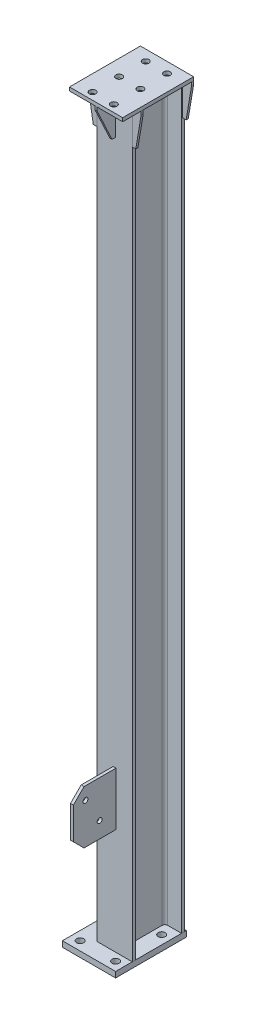
SolidWorks part; units mm, degrees
material "普通碳钢"
ref_plane "前视基准面" through (0, 0, 0) normal (0, 0, 1) x (1, 0, 0)
ref_plane "上视基准面" through (0, 0, 0) normal (0, 1, 0) x (1, 0, 0)
ref_plane "右视基准面" through (0, 0, 0) normal (1, 0, 0) x (0, 0, -1)
sketch "草图1" plane through (0, 0, 0) normal (1, 0, 0) x (0, 0, -1)
  line L0 (-4877.1272, -1126.8159) -> (-4877.1272, -3226.8159)
  dimension "D1" = 2100
other "H型钢 HM150×100(1)"
ref_plane "基准面4" through (-50, -1126.8159, 4951.1272) normal (0, -1, 0) x (1, 0, 0)
sketch "草图11" plane through (-50, -1126.8159, 4951.1272) normal (0, -1, 0) x (1, 0, 0)
  line L0 (-50, -74) -> (50, -74)
  line L1 (50, -74) -> (50, -65)
  line L2 (50, -65) -> (11, -65)
  line L3 (3, -57) -> (3, 57)
  line L4 (11, 65) -> (50, 65)
  line L5 (50, 65) -> (50, 74)
  line L6 (50, 74) -> (-50, 74)
  line L7 (0, 74) -> (0, -74) construction
  line L11 (0, 60) -> (0, 74) construction
  line L14 (-50, -74) -> (-50, -65)
  line L15 (-50, -65) -> (-11, -65)
  line L16 (-3, -57) -> (-3, 57)
  line L17 (-11, 65) -> (-50, 65)
  line L18 (-50, 65) -> (-50, 74)
  arc A2 (11, -65) -> (3, -57) centre (11, -57) cw
  arc A3 (3, 57) -> (11, 65) centre (11, 57) cw
  arc A5 (-11, -65) -> (-3, -57) centre (-11, -57) ccw
  arc A6 (-3, 57) -> (-11, 65) centre (-11, 57) ccw
  point P2 (0, 0)
  point P38 (0, 0)
  point P39 (50, 74)
  point P40 (50, -74)
  point P41 (-50, -74)
  dimension "D8" = 8
  dimension "D1" = 6
  dimension "D2" = 9
  dimension "D3" = 148
  dimension "D4" = 100
  dimension "D9" = 0
sketch "草图12" plane through (0, -3226.8159, 0) normal (0, -1, 0) x (1, 0, 0)
  line L0 (0, 5016.1272) -> (0, 5025.1272) construction
  line L1 (0, 5072.1272) -> (-150, 5072.1272)
  line L2 (0, 5072.1272) -> (0, 4872.1272)
  line L3 (0, 4872.1272) -> (-150, 4872.1272)
  line L4 (-150, 5072.1272) -> (-150, 4872.1272)
  line L5 (-100, 4877.1272) -> (0, 4877.1272) construction
  dimension "D1" = 5
  dimension "D2" = 200
  dimension "D3" = 150
extrude "凸台-拉伸1" add sketch "草图12" along normal blind 16 separate body contours L1 L4 L3 L2
sketch "草图13" plane through (-100, 0, 0) normal (-1, 0, 0) x (0, 0, 1)
  line L0 (5025.1272, -3226.8159) -> (5025.1272, -1126.8159) construction
  line L1 (4877.1272, -1126.8159) -> (5025.1272, -1126.8159)
  line L2 (4877.1272, -1126.8159) -> (4877.1272, -1136.8159)
  line L3 (4877.1272, -1136.8159) -> (5025.1272, -1136.8159)
  line L4 (5025.1272, -1126.8159) -> (5025.1272, -1136.8159)
  dimension "D1" = 10
extrude "切除-拉伸1" cut sketch "草图13" against normal up to vertex (100 mm away) up to point (0, -1126.8159, 4877.1272)
sketch "草图14" plane through (0, -1136.8159, 0) normal (0, 1, 0) x (1, 0, 0)
  line L0 (-100, -4877.1272) -> (-100, -4886.1272) construction
  line L1 (25, -5077.1272) -> (-125, -5077.1272)
  line L2 (25, -5077.1272) -> (25, -4877.1272)
  line L3 (25, -4877.1272) -> (-125, -4877.1272)
  line L4 (-125, -5077.1272) -> (-125, -4877.1272)
  line L5 (0, -4877.1272) -> (-100, -4877.1272) construction
  dimension "D1" = 150
  dimension "D2" = 200
  dimension "D3" = 25
extrude "凸台-拉伸2" add sketch "草图14" along normal blind 10 separate body
sketch "草图16" plane through (0, -1126.8159, 0) normal (0, 1, 0) x (1, 0, 0)
  line L0 (-50, -4877.1272) -> (-50, -5077.1272) construction
  line L1 (25, -4877.1272) -> (-125, -4877.1272) construction
  line L2 (-125, -5077.1272) -> (25, -5077.1272) construction
  line L3 (25, -4907.1272) -> (-125, -4907.1272) construction
  line L4 (25, -5077.1272) -> (25, -4877.1272) construction
  line L5 (-125, -4877.1272) -> (-125, -5077.1272) construction
  line L6 (25, -4982.1272) -> (-125, -4982.1272) construction
  line L7 (25, -5057.1272) -> (4128.0739, -5057.1272) construction
  line L8 (-20, -4877.1272) -> (-20, -5078.3146) construction
  line L9 (-80, -4877.1272) -> (-80, -5078.3146) construction
  circle A0 centre (-20, -4907.1272) radius 9
  circle A1 centre (-20, -4982.1272) radius 9
  circle A2 centre (-20, -5057.1272) radius 9
  circle A3 centre (-80, -4907.1272) radius 9
  circle A4 centre (-80, -4982.1272) radius 9
  circle A5 centre (-80, -5057.1272) radius 9
  dimension "D6" = 18
  dimension "D1" = 30
  dimension "D2" = 30
  dimension "D3" = 30
  dimension "D4" = 75
  dimension "D5" = 75
extrude "切除-拉伸2" cut sketch "草图16" against normal up to next (10 mm away)
sketch "草图17" plane through (0, 0, 4877.1272) normal (0, 0, -1) x (-1, 0, 0)
  line L0 (0, -1136.8159) -> (-25, -1136.8159)
  line L1 (-25, -1136.8159) -> (125, -1136.8159) construction
  line L2 (-25, -1136.8159) -> (-25, -1146.8159)
  line L3 (-25, -1146.8159) -> (-10, -1236.8159)
  line L4 (-10, -1236.8159) -> (0, -1236.8159)
  line L7 (0, -1136.8159) -> (0, -1236.8159)
  line L8 (0, -3226.8159) -> (0, -1136.8159) construction
  line L9 (100, -1136.8159) -> (125, -1136.8159)
  line L10 (125, -1136.8159) -> (125, -1146.8159)
  line L11 (125, -1146.8159) -> (110, -1236.8159)
  line L12 (110, -1236.8159) -> (100, -1236.8159)
  line L13 (100, -3226.8159) -> (100, -1136.8159) construction
  line L14 (100, -1236.8159) -> (100, -1136.8159)
  dimension "D1" = 100
  dimension "D2" = 10
  dimension "D3" = 10
  dimension "D4" = 100
  dimension "D5" = 10
  dimension "D6" = 10
extrude "凸台-拉伸3" add sketch "草图17" against normal blind 6 separate body
sketch "草图18" plane through (0, 0, 5025.1272) normal (0, 0, 1) x (1, 0, 0)
  line L5 (-100, -1236.8159) -> (-100, -1136.8159)
  line L6 (-100, -1136.8159) -> (-125, -1136.8159)
  line L7 (-125, -1136.8159) -> (-125, -1146.8159)
  line L8 (-125, -1146.8159) -> (-110, -1236.8159)
  line L9 (-110, -1236.8159) -> (-100, -1236.8159)
  line L10 (-100, -1236.8159) -> (-100, -1136.8159)
  line L11 (-100, -1136.8159) -> (-125, -1136.8159)
  line L12 (-125, -1136.8159) -> (-125, -1146.8159)
  line L13 (-125, -1146.8159) -> (-110, -1236.8159)
  line L14 (-110, -1236.8159) -> (-100, -1236.8159)
  line L15 (0, -1136.8159) -> (0, -1236.8159)
  line L16 (0, -1236.8159) -> (10, -1236.8159)
  line L17 (10, -1236.8159) -> (25, -1146.8159)
  line L18 (25, -1146.8159) -> (25, -1136.8159)
  line L19 (25, -1136.8159) -> (0, -1136.8159)
  line L20 (0, -1136.8159) -> (0, -1236.8159)
  line L21 (0, -1236.8159) -> (10, -1236.8159)
  line L22 (10, -1236.8159) -> (25, -1146.8159)
  line L23 (25, -1146.8159) -> (25, -1136.8159)
  line L24 (25, -1136.8159) -> (0, -1136.8159)
  dimension "D1" = 0
  dimension "D2" = 0
extrude "凸台-拉伸4" add sketch "草图18" against normal blind 6 separate body
sketch "草图19" plane through (-47, 0, 0) normal (1, 0, 0) x (0, 0, -1)
  line L0 (-5025.1272, -1136.8159) -> (-5077.1272, -1136.8159)
  line L1 (-5077.1272, -1136.8159) -> (-5077.1272, -1146.8159)
  line L2 (-5077.1272, -1146.8159) -> (-5035.1272, -1236.8159)
  line L3 (-5035.1272, -1236.8159) -> (-5025.1272, -1236.8159)
  line L4 (-5025.1272, -1236.8159) -> (-5025.1272, -1146.8159) construction
  line L5 (-5025.1272, -1236.8159) -> (-5025.1272, -1136.8159)
  dimension "D1" = 10
  dimension "D2" = 10
  dimension "D3" = 100
extrude "凸台-拉伸5" add sketch "草图19" against normal up to surface (6 mm away) separate body contours L2 L3 L5 L0 L1 up to face at (-53, -2181.8159, 4951.1272)
sketch "草图20" plane through (0, 0, 5025.1272) normal (0, 0, 1) x (1, 0, 0)
  line L0 (-100, -3226.8159) -> (-100, -1136.8159) construction
  line L1 (-54, -2776.8159) -> (-46, -2776.8159)
  line L2 (-54, -2776.8159) -> (-54, -2926.8159)
  line L3 (-54, -2926.8159) -> (-46, -2926.8159)
  line L4 (-46, -2776.8159) -> (-46, -2926.8159)
  line L5 (0, -3226.8159) -> (-100, -3226.8159) construction
  dimension "D1" = 150
  dimension "D2" = 8
  dimension "D3" = 46
  dimension "D4" = 300
extrude "凸台-拉伸6" add sketch "草图20" along normal blind 120 separate body
chamfer "倒角1" distance 30 angle 45 2 edges at (-50, -2926.8159, 5145.1272) (-50, -2776.8159, 5145.1272)
sketch "草图21" plane through (-46, 0, 0) normal (1, 0, 0) x (0, 0, -1)
  line L0 (-5045.1272, -2926.8159) -> (-5136.3213, -2768.8631) construction
  line L1 (-5115.1272, -2926.8159) -> (-5025.1272, -2926.8159) construction
  line L2 (-5025.1272, -2926.8159) -> (-5025.1272, -2776.8159) construction
  line L5 (-5115.1272, -2881.8159) -> (-5025.1272, -2881.8159)
  line L6 (-5115.1272, -2881.8159) -> (-5025.1272, -2881.8159) construction
  circle A0 centre (-5071.1079, -2881.8159) radius 7
  circle A1 centre (-5111.1079, -2812.5339) radius 7
  dimension "D4" = 14
  dimension "D5" = 14
  dimension "D1" = 60
  dimension "D2" = 20
  dimension "D6" = 80
  dimension "D3" = 45
extrude "切除-拉伸3" cut sketch "草图21" against normal up to next (8 mm away)
sketch "草图22" plane through (0, 0, 4886.1272) normal (0, 0, 1) x (1, 0, 0)
  line L0 (-61, -3226.8159) -> (-61, -1136.8159) construction
  line L1 (-61, -2826.8159) -> (-220, -2826.8159)
  line L2 (-61, -2826.8159) -> (-61, -2976.8159)
  line L3 (-61, -2976.8159) -> (-220, -2976.8159)
  line L4 (-220, -2826.8159) -> (-220, -2976.8159)
  line L5 (-100, -3226.8159) -> (-100, -1136.8159) construction
  line L6 (-61, -3226.8159) -> (-100, -3226.8159) construction
  dimension "D1" = 120
  dimension "D2" = 150
  dimension "D3" = 250
extrude "凸台-拉伸7" add sketch "草图22" along normal blind 8 separate body
chamfer "倒角2" distance 30 angle 45 2 edges at (-220, -2976.8159, 4890.1272) (-220, -2826.8159, 4890.1272)
sketch "草图23" plane through (0, 0, 4894.1272) normal (0, 0, 1) x (1, 0, 0)
  line L0 (-100, -2976.8159) -> (-1212.1791, -1388.4595) construction
  line L1 (-190, -2976.8159) -> (-61, -2976.8159) construction
  line L4 (-100, -3226.8159) -> (-100, -1136.8159) construction
  line L5 (-190, -2936.8159) -> (-61, -2936.8159)
  line L6 (-190, -2936.8159) -> (-61, -2936.8159) construction
  circle A0 centre (-128.0083, -2936.8159) radius 7
  circle A1 centre (-173.8944, -2871.2837) radius 7
  dimension "D3" = 14
  dimension "D4" = 14
  dimension "D5" = 80
  dimension "D6" = 55
  dimension "D2" = 40
extrude "切除-拉伸4" cut sketch "草图23" against normal up to next (8 mm away)
sketch "草图24" plane through (0, -3242.8159, 0) normal (0, -1, 0) x (1, 0, 0)
  line L0 (-125, 5047.1272) -> (-25, 5047.1272) construction
  line L1 (-25, 5047.1272) -> (-25, 4917.1272) construction
  line L2 (-25, 4917.1272) -> (-125, 4917.1272) construction
  line L3 (-125, 4917.1272) -> (-125, 5047.1272) construction
  line L4 (0, 5072.1272) -> (-150, 5072.1272) construction
  line L5 (0, 5072.1272) -> (0, 4872.1272) construction
  circle A0 centre (-125, 5047.1272) radius 10
  circle A1 centre (-25, 5047.1272) radius 10
  circle A2 centre (-125, 4917.1272) radius 10
  circle A3 centre (-25, 4917.1272) radius 10
  dimension "D5" = 20
  dimension "D1" = 100
  dimension "D2" = 130
  dimension "D3" = 25
  dimension "D4" = 25
extrude "切除-拉伸5" cut sketch "草图24" against normal up to next (16 mm away)
